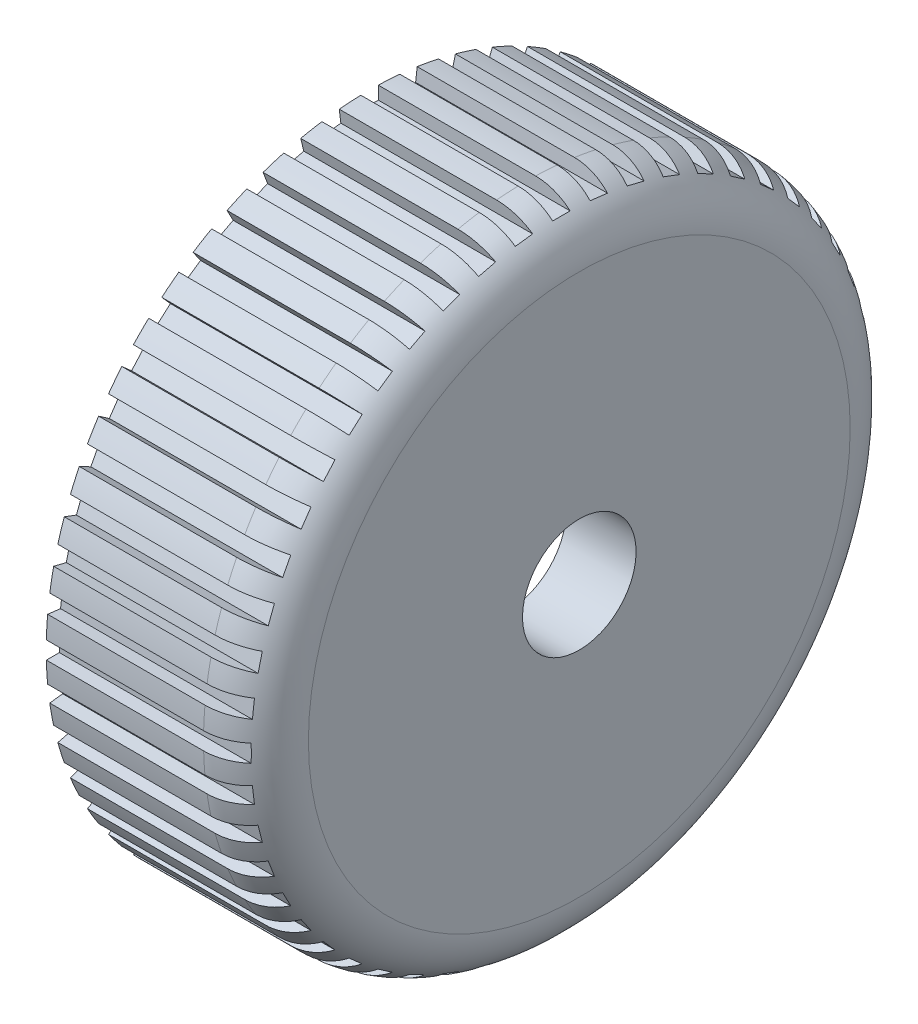
SolidWorks part; units mm, degrees
ref_plane "Спереди" through (0, 0, 0) normal (0, 0, 1) x (1, 0, 0)
ref_plane "Сверху" through (0, 0, 0) normal (0, 1, 0) x (1, 0, 0)
ref_plane "Справа" through (0, 0, 0) normal (1, 0, 0) x (0, 0, -1)
sketch "Эскиз1" plane through (0, 0, 0) normal (0, 0, 1) x (1, 0, 0)
  line L0 (0, 37) -> (0, 30.3)
  line L1 (0, 30.3) -> (16, 30.3)
  line L2 (16, 30.3) -> (16, 6.5)
  line L3 (16, 6.5) -> (24, 6.5)
  line L4 (24, 6.5) -> (24, 31)
  line L5 (18, 37) -> (0, 37)
  line L6 (0, 30.3) -> (0, 0) construction
  line L7 (0, 0) -> (24, 0) construction
  line L8 (24, 0) -> (24, 6.5) construction
  arc A0 (24, 31) -> (18, 37) centre (18, 31) ccw
  dimension "D6" = 6
  dimension "D1" = 60.6
  dimension "D2" = 74
  dimension "D3" = 8
  dimension "D4" = 16
  dimension "D5" = 13
revolve "Повернуть1" add sketch "Эскиз1" angle 360 about L7
sketch "Эскиз2" plane through (0, 0, 0) normal (-1, 0, 0) x (0, 0, 1)
  line L0 (0, 35.5) -> (0, 0) construction
  line L1 (-1, 38.5) -> (1, 38.5)
  line L2 (-1, 38.5) -> (-1, 35.5)
  line L3 (-1, 35.5) -> (1, 35.5)
  line L4 (1, 38.5) -> (1, 35.5)
  line L5 (5.6334, 38.0988) -> (5.2718, 35.1206)
  line L6 (3.648, 38.3398) -> (3.2863, 35.3617)
  line L7 (3.648, 38.3398) -> (5.6334, 38.0988)
  line L8 (3.2863, 35.3617) -> (5.2718, 35.1206)
  line L9 (10.1846, 37.1419) -> (9.4666, 34.2291)
  line L10 (8.2427, 37.6206) -> (7.5248, 34.7078)
  line L11 (8.2427, 37.6206) -> (10.1846, 37.1419)
  line L12 (7.5248, 34.7078) -> (9.4666, 34.2291)
  line L13 (14.5873, 35.6435) -> (13.5235, 32.8385)
  line L14 (12.7173, 36.3527) -> (11.6535, 33.5477)
  line L15 (12.7173, 36.3527) -> (14.5873, 35.6435)
  line L16 (11.6535, 33.5477) -> (13.5235, 32.8385)
  line L17 (18.7773, 33.6253) -> (17.3831, 30.969)
  line L18 (17.0064, 34.5548) -> (15.6122, 31.8984)
  line L19 (17.0064, 34.5548) -> (18.7773, 33.6253)
  line L20 (15.6122, 31.8984) -> (17.3831, 30.969)
  line L21 (22.6935, 31.1168) -> (20.9893, 28.6479)
  line L22 (21.0475, 32.2529) -> (19.3433, 29.784)
  line L23 (21.0475, 32.2529) -> (22.6935, 31.1168)
  line L24 (19.3433, 29.784) -> (20.9893, 28.6479)
  line L25 (26.2787, 28.1545) -> (24.2894, 25.909)
  line L26 (24.7817, 29.4808) -> (22.7923, 27.2353)
  line L27 (24.7817, 29.4808) -> (26.2787, 28.1545)
  line L28 (22.7923, 27.2353) -> (24.2894, 25.909)
  line L29 (29.4808, 24.7817) -> (27.2353, 22.7923)
  line L30 (28.1545, 26.2787) -> (25.909, 24.2894)
  line L31 (28.1545, 26.2787) -> (29.4808, 24.7817)
  line L32 (25.909, 24.2894) -> (27.2353, 22.7923)
  line L33 (32.2529, 21.0475) -> (29.784, 19.3433)
  line L34 (31.1168, 22.6935) -> (28.6479, 20.9893)
  line L35 (31.1168, 22.6935) -> (32.2529, 21.0475)
  line L36 (28.6479, 20.9893) -> (29.784, 19.3433)
  line L37 (34.5548, 17.0064) -> (31.8984, 15.6122)
  line L38 (33.6253, 18.7773) -> (30.969, 17.3831)
  line L39 (33.6253, 18.7773) -> (34.5548, 17.0064)
  line L40 (30.969, 17.3831) -> (31.8984, 15.6122)
  line L41 (36.3527, 12.7173) -> (33.5477, 11.6535)
  line L42 (35.6435, 14.5873) -> (32.8385, 13.5235)
  line L43 (35.6435, 14.5873) -> (36.3527, 12.7173)
  line L44 (32.8385, 13.5235) -> (33.5477, 11.6535)
  line L45 (37.6206, 8.2427) -> (34.7078, 7.5248)
  line L46 (37.1419, 10.1846) -> (34.2291, 9.4666)
  line L47 (37.1419, 10.1846) -> (37.6206, 8.2427)
  line L48 (34.2291, 9.4666) -> (34.7078, 7.5248)
  line L49 (38.3398, 3.648) -> (35.3617, 3.2863)
  line L50 (38.0988, 5.6334) -> (35.1206, 5.2718)
  line L51 (38.0988, 5.6334) -> (38.3398, 3.648)
  line L52 (35.1206, 5.2718) -> (35.3617, 3.2863)
  line L53 (38.5, -1) -> (35.5, -1)
  line L54 (38.5, 1) -> (35.5, 1)
  line L55 (38.5, 1) -> (38.5, -1)
  line L56 (35.5, 1) -> (35.5, -1)
  line L57 (38.0988, -5.6334) -> (35.1206, -5.2718)
  line L58 (38.3398, -3.648) -> (35.3617, -3.2863)
  line L59 (38.3398, -3.648) -> (38.0988, -5.6334)
  line L60 (35.3617, -3.2863) -> (35.1206, -5.2718)
  line L61 (37.1419, -10.1846) -> (34.2291, -9.4666)
  line L62 (37.6206, -8.2427) -> (34.7078, -7.5248)
  line L63 (37.6206, -8.2427) -> (37.1419, -10.1846)
  line L64 (34.7078, -7.5248) -> (34.2291, -9.4666)
  line L65 (35.6435, -14.5873) -> (32.8385, -13.5235)
  line L66 (36.3527, -12.7173) -> (33.5477, -11.6535)
  line L67 (36.3527, -12.7173) -> (35.6435, -14.5873)
  line L68 (33.5477, -11.6535) -> (32.8385, -13.5235)
  line L69 (33.6253, -18.7773) -> (30.969, -17.3831)
  line L70 (34.5548, -17.0064) -> (31.8984, -15.6122)
  line L71 (34.5548, -17.0064) -> (33.6253, -18.7773)
  line L72 (31.8984, -15.6122) -> (30.969, -17.3831)
  line L73 (31.1168, -22.6935) -> (28.6479, -20.9893)
  line L74 (32.2529, -21.0475) -> (29.784, -19.3433)
  line L75 (32.2529, -21.0475) -> (31.1168, -22.6935)
  line L76 (29.784, -19.3433) -> (28.6479, -20.9893)
  line L77 (28.1545, -26.2787) -> (25.909, -24.2894)
  line L78 (29.4808, -24.7817) -> (27.2353, -22.7923)
  line L79 (29.4808, -24.7817) -> (28.1545, -26.2787)
  line L80 (27.2353, -22.7923) -> (25.909, -24.2894)
  line L81 (24.7817, -29.4808) -> (22.7923, -27.2353)
  line L82 (26.2787, -28.1545) -> (24.2894, -25.909)
  line L83 (26.2787, -28.1545) -> (24.7817, -29.4808)
  line L84 (24.2894, -25.909) -> (22.7923, -27.2353)
  line L85 (21.0475, -32.2529) -> (19.3433, -29.784)
  line L86 (22.6935, -31.1168) -> (20.9893, -28.6479)
  line L87 (22.6935, -31.1168) -> (21.0475, -32.2529)
  line L88 (20.9893, -28.6479) -> (19.3433, -29.784)
  line L89 (17.0064, -34.5548) -> (15.6122, -31.8984)
  line L90 (18.7773, -33.6253) -> (17.3831, -30.969)
  line L91 (18.7773, -33.6253) -> (17.0064, -34.5548)
  line L92 (17.3831, -30.969) -> (15.6122, -31.8984)
  line L93 (12.7173, -36.3527) -> (11.6535, -33.5477)
  line L94 (14.5873, -35.6435) -> (13.5235, -32.8385)
  line L95 (14.5873, -35.6435) -> (12.7173, -36.3527)
  line L96 (13.5235, -32.8385) -> (11.6535, -33.5477)
  line L97 (8.2427, -37.6206) -> (7.5248, -34.7078)
  line L98 (10.1846, -37.1419) -> (9.4666, -34.2291)
  line L99 (10.1846, -37.1419) -> (8.2427, -37.6206)
  line L100 (9.4666, -34.2291) -> (7.5248, -34.7078)
  line L101 (3.648, -38.3398) -> (3.2863, -35.3617)
  line L102 (5.6334, -38.0988) -> (5.2718, -35.1206)
  line L103 (5.6334, -38.0988) -> (3.648, -38.3398)
  line L104 (5.2718, -35.1206) -> (3.2863, -35.3617)
  line L105 (-1, -38.5) -> (-1, -35.5)
  line L106 (1, -38.5) -> (1, -35.5)
  line L107 (1, -38.5) -> (-1, -38.5)
  line L108 (1, -35.5) -> (-1, -35.5)
  line L109 (-5.6334, -38.0988) -> (-5.2718, -35.1206)
  line L110 (-3.648, -38.3398) -> (-3.2863, -35.3617)
  line L111 (-3.648, -38.3398) -> (-5.6334, -38.0988)
  line L112 (-3.2863, -35.3617) -> (-5.2718, -35.1206)
  line L113 (-10.1846, -37.1419) -> (-9.4666, -34.2291)
  line L114 (-8.2427, -37.6206) -> (-7.5248, -34.7078)
  line L115 (-8.2427, -37.6206) -> (-10.1846, -37.1419)
  line L116 (-7.5248, -34.7078) -> (-9.4666, -34.2291)
  line L117 (-14.5873, -35.6435) -> (-13.5235, -32.8385)
  line L118 (-12.7173, -36.3527) -> (-11.6535, -33.5477)
  line L119 (-12.7173, -36.3527) -> (-14.5873, -35.6435)
  line L120 (-11.6535, -33.5477) -> (-13.5235, -32.8385)
  line L121 (-18.7773, -33.6253) -> (-17.3831, -30.969)
  line L122 (-17.0064, -34.5548) -> (-15.6122, -31.8984)
  line L123 (-17.0064, -34.5548) -> (-18.7773, -33.6253)
  line L124 (-15.6122, -31.8984) -> (-17.3831, -30.969)
  line L125 (-22.6935, -31.1168) -> (-20.9893, -28.6479)
  line L126 (-21.0475, -32.2529) -> (-19.3433, -29.784)
  line L127 (-21.0475, -32.2529) -> (-22.6935, -31.1168)
  line L128 (-19.3433, -29.784) -> (-20.9893, -28.6479)
  line L129 (-26.2787, -28.1545) -> (-24.2894, -25.909)
  line L130 (-24.7817, -29.4808) -> (-22.7923, -27.2353)
  line L131 (-24.7817, -29.4808) -> (-26.2787, -28.1545)
  line L132 (-22.7923, -27.2353) -> (-24.2894, -25.909)
  line L133 (-29.4808, -24.7817) -> (-27.2353, -22.7923)
  line L134 (-28.1545, -26.2787) -> (-25.909, -24.2894)
  line L135 (-28.1545, -26.2787) -> (-29.4808, -24.7817)
  line L136 (-25.909, -24.2894) -> (-27.2353, -22.7923)
  line L137 (-32.2529, -21.0475) -> (-29.784, -19.3433)
  line L138 (-31.1168, -22.6935) -> (-28.6479, -20.9893)
  line L139 (-31.1168, -22.6935) -> (-32.2529, -21.0475)
  line L140 (-28.6479, -20.9893) -> (-29.784, -19.3433)
  line L141 (-34.5548, -17.0064) -> (-31.8984, -15.6122)
  line L142 (-33.6253, -18.7773) -> (-30.969, -17.3831)
  line L143 (-33.6253, -18.7773) -> (-34.5548, -17.0064)
  line L144 (-30.969, -17.3831) -> (-31.8984, -15.6122)
  line L145 (-36.3527, -12.7173) -> (-33.5477, -11.6535)
  line L146 (-35.6435, -14.5873) -> (-32.8385, -13.5235)
  line L147 (-35.6435, -14.5873) -> (-36.3527, -12.7173)
  line L148 (-32.8385, -13.5235) -> (-33.5477, -11.6535)
  line L149 (-37.6206, -8.2427) -> (-34.7078, -7.5248)
  line L150 (-37.1419, -10.1846) -> (-34.2291, -9.4666)
  line L151 (-37.1419, -10.1846) -> (-37.6206, -8.2427)
  line L152 (-34.2291, -9.4666) -> (-34.7078, -7.5248)
  line L153 (-38.3398, -3.648) -> (-35.3617, -3.2863)
  line L154 (-38.0988, -5.6334) -> (-35.1206, -5.2718)
  line L155 (-38.0988, -5.6334) -> (-38.3398, -3.648)
  line L156 (-35.1206, -5.2718) -> (-35.3617, -3.2863)
  line L157 (-38.5, 1) -> (-35.5, 1)
  line L158 (-38.5, -1) -> (-35.5, -1)
  line L159 (-38.5, -1) -> (-38.5, 1)
  line L160 (-35.5, -1) -> (-35.5, 1)
  line L161 (-38.0988, 5.6334) -> (-35.1206, 5.2718)
  line L162 (-38.3398, 3.648) -> (-35.3617, 3.2863)
  line L163 (-38.3398, 3.648) -> (-38.0988, 5.6334)
  line L164 (-35.3617, 3.2863) -> (-35.1206, 5.2718)
  line L165 (-37.1419, 10.1846) -> (-34.2291, 9.4666)
  line L166 (-37.6206, 8.2427) -> (-34.7078, 7.5248)
  line L167 (-37.6206, 8.2427) -> (-37.1419, 10.1846)
  line L168 (-34.7078, 7.5248) -> (-34.2291, 9.4666)
  line L169 (-35.6435, 14.5873) -> (-32.8385, 13.5235)
  line L170 (-36.3527, 12.7173) -> (-33.5477, 11.6535)
  line L171 (-36.3527, 12.7173) -> (-35.6435, 14.5873)
  line L172 (-33.5477, 11.6535) -> (-32.8385, 13.5235)
  line L173 (-33.6253, 18.7773) -> (-30.969, 17.3831)
  line L174 (-34.5548, 17.0064) -> (-31.8984, 15.6122)
  line L175 (-34.5548, 17.0064) -> (-33.6253, 18.7773)
  line L176 (-31.8984, 15.6122) -> (-30.969, 17.3831)
  line L177 (-31.1168, 22.6935) -> (-28.6479, 20.9893)
  line L178 (-32.2529, 21.0475) -> (-29.784, 19.3433)
  line L179 (-32.2529, 21.0475) -> (-31.1168, 22.6935)
  line L180 (-29.784, 19.3433) -> (-28.6479, 20.9893)
  line L181 (-28.1545, 26.2787) -> (-25.909, 24.2894)
  line L182 (-29.4808, 24.7817) -> (-27.2353, 22.7923)
  line L183 (-29.4808, 24.7817) -> (-28.1545, 26.2787)
  line L184 (-27.2353, 22.7923) -> (-25.909, 24.2894)
  line L185 (-24.7817, 29.4808) -> (-22.7923, 27.2353)
  line L186 (-26.2787, 28.1545) -> (-24.2894, 25.909)
  line L187 (-26.2787, 28.1545) -> (-24.7817, 29.4808)
  line L188 (-24.2894, 25.909) -> (-22.7923, 27.2353)
  line L189 (-21.0475, 32.2529) -> (-19.3433, 29.784)
  line L190 (-22.6935, 31.1168) -> (-20.9893, 28.6479)
  line L191 (-22.6935, 31.1168) -> (-21.0475, 32.2529)
  line L192 (-20.9893, 28.6479) -> (-19.3433, 29.784)
  line L193 (-17.0064, 34.5548) -> (-15.6122, 31.8984)
  line L194 (-18.7773, 33.6253) -> (-17.3831, 30.969)
  line L195 (-18.7773, 33.6253) -> (-17.0064, 34.5548)
  line L196 (-17.3831, 30.969) -> (-15.6122, 31.8984)
  line L197 (-12.7173, 36.3527) -> (-11.6535, 33.5477)
  line L198 (-14.5873, 35.6435) -> (-13.5235, 32.8385)
  line L199 (-14.5873, 35.6435) -> (-12.7173, 36.3527)
  line L200 (-13.5235, 32.8385) -> (-11.6535, 33.5477)
  line L201 (-8.2427, 37.6206) -> (-7.5248, 34.7078)
  line L202 (-10.1846, 37.1419) -> (-9.4666, 34.2291)
  line L203 (-10.1846, 37.1419) -> (-8.2427, 37.6206)
  line L204 (-9.4666, 34.2291) -> (-7.5248, 34.7078)
  line L205 (-3.648, 38.3398) -> (-3.2863, 35.3617)
  line L206 (-5.6334, 38.0988) -> (-5.2718, 35.1206)
  line L207 (-5.6334, 38.0988) -> (-3.648, 38.3398)
  line L208 (-5.2718, 35.1206) -> (-3.2863, 35.3617)
  point P213 (0, 0)
  dimension "D1" = 2
  dimension "D2" = 35.5
  dimension "D3" = 3
extrude "Вырез-Вытянуть2" cut sketch "Эскиз2" against normal through all
